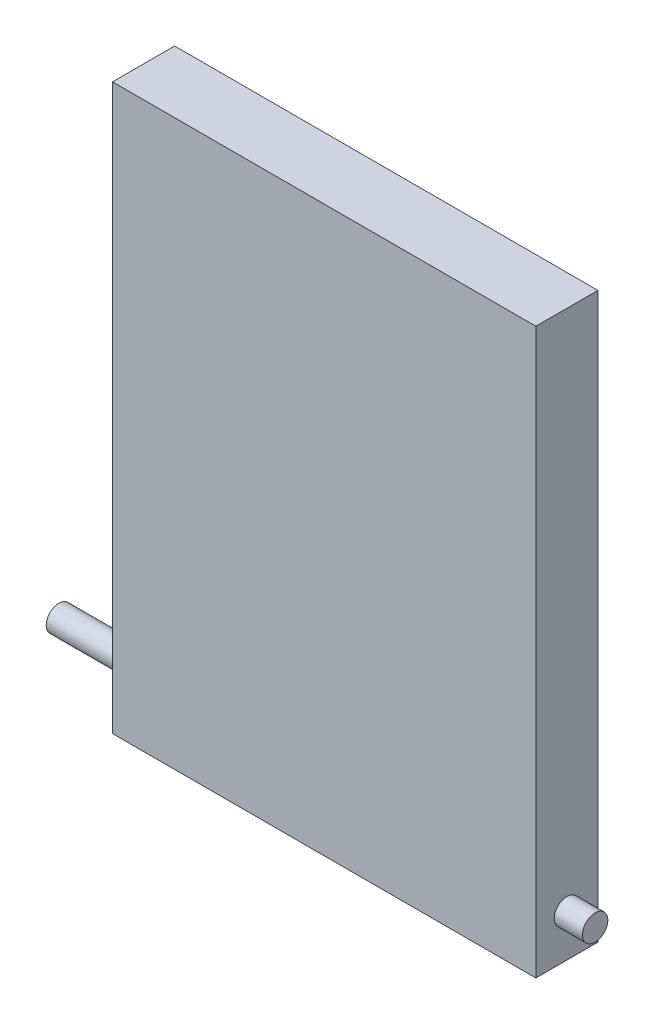
SolidWorks part; units mm, degrees
ref_plane "Plan de face" through (0, 0, 0) normal (0, 0, 1) x (1, 0, 0)
ref_plane "Plan de dessus" through (0, 0, 0) normal (0, 1, 0) x (1, 0, 0)
ref_plane "Plan de droite" through (0, 0, 0) normal (1, 0, 0) x (0, 0, -1)
sketch "Esquisse1" plane through (0, 0, 0) normal (0, 0, 1) x (1, 0, 0)
  line L1 (0, 0) -> (150, 0)
  line L2 (0, 0) -> (0, 200)
  line L3 (0, 200) -> (150, 200)
  line L4 (150, 0) -> (150, 200)
  dimension "D1" = 200
  dimension "D2" = 150
extrude "Extrusion1" add sketch "Esquisse1" along normal blind 22
sketch "Esquisse2" plane through (0, 0, 0) normal (-1, 0, 0) x (0, 0, 1)
  line L0 (11, 0) -> (11, 200) construction
  line L1 (22, 0) -> (0, 0) construction
  line L2 (22, 200) -> (0, 200) construction
  line L3 (11, 200) -> (-26.0984, 187.6903) construction
  circle A0 centre (11, 15) radius 4.5
  dimension "D2" = 9
  dimension "D1" = 15
extrude "Extrusion2" add sketch "Esquisse2" along normal blind 30 and the other way blind 160
